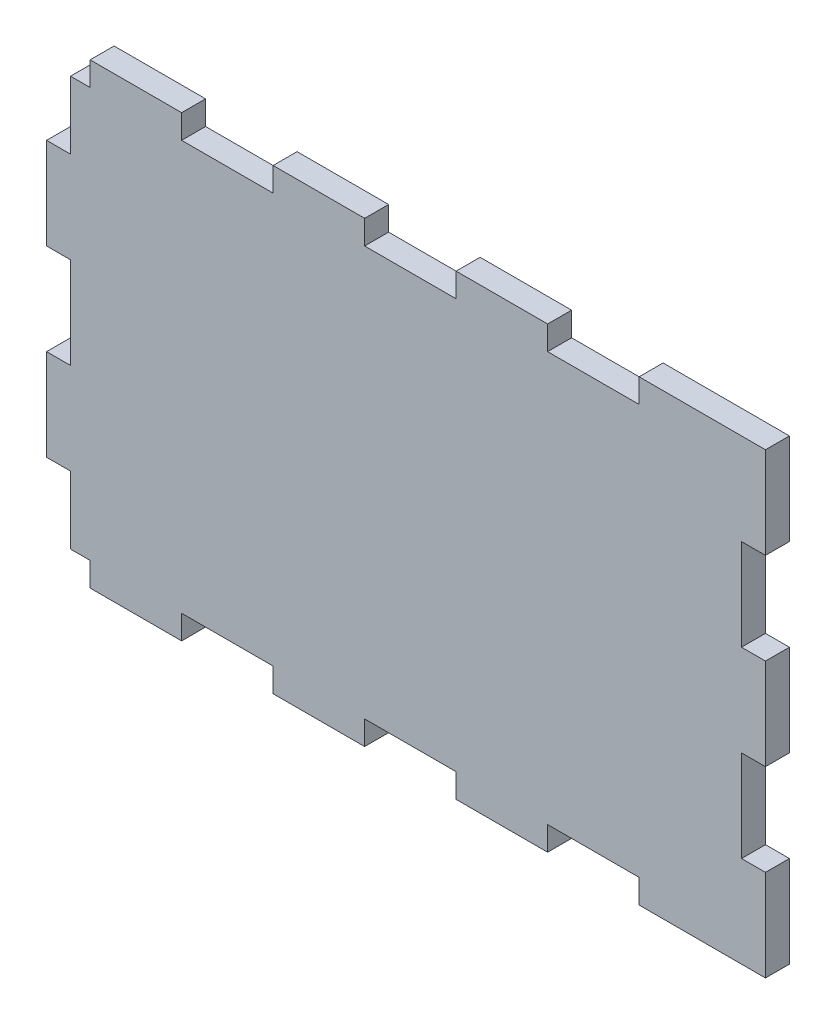
SolidWorks part; units mm, degrees
ref_plane "Alzado" through (0, 0, 0) normal (0, 0, 1) x (1, 0, 0)
ref_plane "Planta" through (0, 0, 0) normal (0, 1, 0) x (1, 0, 0)
ref_plane "Vista lateral" through (0, 0, 0) normal (1, 0, 0) x (0, 0, -1)
sketch "Croquis1" plane through (0, 0, 0) normal (0, 0, 1) x (1, 0, 0)
  line L11 (-57, -53.355) -> (-52.5, -53.355)
  line L12 (-52.5, -53.355) -> (-52.5, -56.355)
  line L13 (-52.5, -56.355) -> (-31.5, -56.355)
  line L14 (-31.5, -56.355) -> (-31.5, -53.355)
  line L15 (-31.5, -53.355) -> (-10.5, -53.355)
  line L16 (-10.5, -53.355) -> (-10.5, -56.355)
  line L17 (-10.5, -56.355) -> (10.5, -56.355)
  line L18 (10.5, -56.355) -> (10.5, -53.355)
  line L19 (10.5, -53.355) -> (31.5, -53.355)
  line L20 (31.5, -53.355) -> (31.5, -56.355)
  line L21 (31.5, -56.355) -> (52.5, -56.355)
  line L22 (52.5, -56.355) -> (52.5, -53.355)
  line L23 (52.5, -53.355) -> (73.5, -53.355)
  line L24 (73.5, -53.355) -> (73.5, -56.355)
  line L25 (73.5, -56.355) -> (94.5, -56.355)
  line L26 (94.5, -56.355) -> (100, -56.355)
  line L27 (100, -56.355) -> (100, -37.855)
  line L28 (100, -37.855) -> (97, -37.855)
  line L29 (97, -37.855) -> (97, -16.855)
  line L30 (97, -16.855) -> (100, -16.855)
  line L31 (100, -16.855) -> (100, 4.145)
  line L32 (100, 4.145) -> (97, 4.145)
  line L33 (97, 4.145) -> (97, 25.145)
  line L34 (97, 25.145) -> (100, 25.145)
  line L35 (100, 25.145) -> (100, 43.645)
  line L36 (100, 43.645) -> (73.5, 43.645)
  line L37 (73.5, 43.645) -> (73.5, 40.645)
  line L38 (73.5, 40.645) -> (52.5, 40.645)
  line L39 (52.5, 40.645) -> (52.5, 43.645)
  line L40 (52.5, 43.645) -> (31.5, 43.645)
  line L41 (31.5, 43.645) -> (31.5, 40.645)
  line L42 (31.5, 40.645) -> (10.5, 40.645)
  line L43 (10.5, 40.645) -> (10.5, 43.645)
  line L44 (10.5, 43.645) -> (-10.5, 43.645)
  line L45 (-10.5, 43.645) -> (-10.5, 40.645)
  line L46 (-10.5, 40.645) -> (-31.5, 40.645)
  line L47 (-31.5, 40.645) -> (-31.5, 43.645)
  line L48 (-31.5, 43.645) -> (-52.5, 43.645)
  line L49 (-52.5, 43.645) -> (-52.5, 40.645)
  line L50 (-52.5, 40.645) -> (-57, 40.645)
  line L54 (-60, 25.145) -> (-57, 25.145)
  line L55 (-57, 25.145) -> (-57, 40.645)
  line L56 (-60, 4.145) -> (-57, 4.145)
  line L60 (-60, 25.145) -> (-60, 4.145)
  line L61 (-57, 4.145) -> (-57, -16.855)
  line L62 (-57, -16.855) -> (-60, -16.855)
  line L64 (-60, -16.855) -> (-60, -37.855)
  line L67 (-57, -37.855) -> (-57, -53.355)
  line L68 (-60, -37.855) -> (-57, -37.855)
  dimension "D1" = 21
extrude "Saliente-Extruir1" add sketch "Croquis1" along normal blind 5.5
sketch "Croquis2" plane through (0, 43.645, 0) normal (0, 1, 0) x (1, 0, 0)
  line L0 (100, 0) -> (73.5, 0) construction
  line L1 (73.5, 0) -> (73.5, -5.5) construction
  line L2 (73.5, -5.5) -> (100, -5.5) construction
  line L3 (100, -5.5) -> (100, 0) construction
  line L4 (52.5, 0) -> (31.5, 0) construction
  line L5 (31.5, 0) -> (31.5, -5.5) construction
  line L6 (31.5, -5.5) -> (52.5, -5.5) construction
  line L7 (52.5, -5.5) -> (52.5, 0) construction
  line L8 (10.5, 0) -> (-10.5, 0) construction
  line L9 (-10.5, 0) -> (-10.5, -5.5) construction
  line L10 (-10.5, -5.5) -> (10.5, -5.5) construction
  line L11 (10.5, -5.5) -> (10.5, 0) construction
  line L12 (-31.5, 0) -> (-52.5, 0) construction
  line L13 (-52.5, 0) -> (-52.5, -5.5) construction
  line L14 (-52.5, -5.5) -> (-31.5, -5.5) construction
  line L15 (-31.5, -5.5) -> (-31.5, 0) construction
  line L16 (100, 0) -> (73.5, 0)
  line L17 (73.5, 0) -> (73.5, -5.5)
  line L18 (73.5, -5.5) -> (100, -5.5)
  line L19 (100, -5.5) -> (100, 0)
  line L20 (52.5, 0) -> (31.5, 0)
  line L21 (31.5, 0) -> (31.5, -5.5)
  line L22 (31.5, -5.5) -> (52.5, -5.5)
  line L23 (52.5, -5.5) -> (52.5, 0)
  line L24 (10.5, 0) -> (-10.5, 0)
  line L25 (-10.5, 0) -> (-10.5, -5.5)
  line L26 (-10.5, -5.5) -> (10.5, -5.5)
  line L27 (10.5, -5.5) -> (10.5, 0)
  line L28 (-31.5, 0) -> (-52.5, 0)
  line L29 (-52.5, 0) -> (-52.5, -5.5)
  line L30 (-52.5, -5.5) -> (-31.5, -5.5)
  line L31 (-31.5, -5.5) -> (-31.5, 0)
extrude "Saliente-Extruir2" add sketch "Croquis2" along normal blind 2.5
sketch "Croquis3" plane through (100, 0, 0) normal (1, 0, 0) x (0, 0, -1)
  line L0 (0, -56.355) -> (0, -37.855) construction
  line L1 (0, -37.855) -> (-5.5, -37.855) construction
  line L2 (-5.5, -37.855) -> (-5.5, -56.355) construction
  line L3 (-5.5, -56.355) -> (0, -56.355) construction
  line L4 (0, -16.855) -> (0, 4.145) construction
  line L5 (0, 4.145) -> (-5.5, 4.145) construction
  line L6 (-5.5, 4.145) -> (-5.5, -16.855) construction
  line L7 (-5.5, -16.855) -> (0, -16.855) construction
  line L8 (0, 25.145) -> (0, 46.145) construction
  line L9 (0, 46.145) -> (-5.5, 46.145) construction
  line L10 (-5.5, 46.145) -> (-5.5, 25.145) construction
  line L11 (-5.5, 25.145) -> (0, 25.145) construction
  line L12 (0, -56.355) -> (0, -37.855)
  line L13 (0, -37.855) -> (-5.5, -37.855)
  line L14 (-5.5, -37.855) -> (-5.5, -56.355)
  line L15 (-5.5, -56.355) -> (0, -56.355)
  line L16 (0, -16.855) -> (0, 4.145)
  line L17 (0, 4.145) -> (-5.5, 4.145)
  line L18 (-5.5, 4.145) -> (-5.5, -16.855)
  line L19 (-5.5, -16.855) -> (0, -16.855)
  line L20 (0, 25.145) -> (0, 46.145)
  line L21 (0, 46.145) -> (-5.5, 46.145)
  line L22 (-5.5, 46.145) -> (-5.5, 25.145)
  line L23 (-5.5, 25.145) -> (0, 25.145)
extrude "Saliente-Extruir3" add sketch "Croquis3" along normal blind 2.5
sketch "Croquis4" plane through (0, -56.355, 0) normal (0, -1, 0) x (1, 0, 0)
  line L0 (-52.5, 0) -> (-31.5, 0) construction
  line L1 (-31.5, 0) -> (-31.5, 5.5) construction
  line L2 (-31.5, 5.5) -> (-52.5, 5.5) construction
  line L3 (-52.5, 5.5) -> (-52.5, 0) construction
  line L4 (-10.5, 0) -> (10.5, 0) construction
  line L5 (10.5, 0) -> (10.5, 5.5) construction
  line L6 (10.5, 5.5) -> (-10.5, 5.5) construction
  line L7 (-10.5, 5.5) -> (-10.5, 0) construction
  line L8 (31.5, 0) -> (52.5, 0) construction
  line L9 (52.5, 0) -> (52.5, 5.5) construction
  line L10 (52.5, 5.5) -> (31.5, 5.5) construction
  line L11 (31.5, 5.5) -> (31.5, 0) construction
  line L12 (73.5, 0) -> (102.5, 0) construction
  line L13 (102.5, 0) -> (102.5, 5.5) construction
  line L14 (102.5, 5.5) -> (73.5, 5.5) construction
  line L15 (73.5, 5.5) -> (73.5, 0) construction
  line L16 (-52.5, 0) -> (-31.5, 0)
  line L17 (-31.5, 0) -> (-31.5, 5.5)
  line L18 (-31.5, 5.5) -> (-52.5, 5.5)
  line L19 (-52.5, 5.5) -> (-52.5, 0)
  line L20 (-10.5, 0) -> (10.5, 0)
  line L21 (10.5, 0) -> (10.5, 5.5)
  line L22 (10.5, 5.5) -> (-10.5, 5.5)
  line L23 (-10.5, 5.5) -> (-10.5, 0)
  line L24 (31.5, 0) -> (52.5, 0)
  line L25 (52.5, 0) -> (52.5, 5.5)
  line L26 (52.5, 5.5) -> (31.5, 5.5)
  line L27 (31.5, 5.5) -> (31.5, 0)
  line L28 (73.5, 0) -> (102.5, 0)
  line L29 (102.5, 0) -> (102.5, 5.5)
  line L30 (102.5, 5.5) -> (73.5, 5.5)
  line L31 (73.5, 5.5) -> (73.5, 0)
extrude "Saliente-Extruir4" add sketch "Croquis4" along normal blind 2.5
sketch "Croquis5" plane through (-60, 0, 0) normal (-1, 0, 0) x (0, 0, 1)
  line L0 (0, -16.855) -> (0, -37.855) construction
  line L1 (0, -37.855) -> (5.5, -37.855) construction
  line L2 (5.5, -37.855) -> (5.5, -16.855) construction
  line L3 (5.5, -16.855) -> (0, -16.855) construction
  line L4 (0, 25.145) -> (0, 4.145) construction
  line L5 (0, 4.145) -> (5.5, 4.145) construction
  line L6 (5.5, 4.145) -> (5.5, 25.145) construction
  line L7 (5.5, 25.145) -> (0, 25.145) construction
  line L8 (0, -16.855) -> (0, -37.855)
  line L9 (0, -37.855) -> (5.5, -37.855)
  line L10 (5.5, -37.855) -> (5.5, -16.855)
  line L11 (5.5, -16.855) -> (0, -16.855)
  line L12 (0, 25.145) -> (0, 4.145)
  line L13 (0, 4.145) -> (5.5, 4.145)
  line L14 (5.5, 4.145) -> (5.5, 25.145)
  line L15 (5.5, 25.145) -> (0, 25.145)
extrude "Saliente-Extruir5" add sketch "Croquis5" along normal blind 2.5
